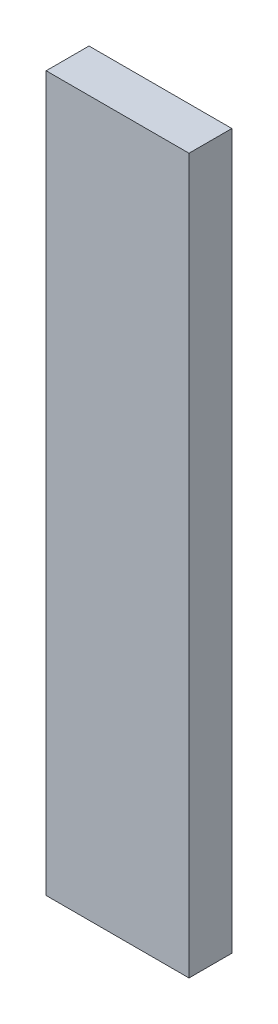
SolidWorks part; units mm, degrees
ref_plane "Alzado" through (0, 0, 0) normal (0, 0, 1) x (1, 0, 0)
ref_plane "Planta" through (0, 0, 0) normal (0, 1, 0) x (1, 0, 0)
ref_plane "Vista lateral" through (0, 0, 0) normal (1, 0, 0) x (0, 0, -1)
sketch "Model" plane through (0, 0, 0) normal (0, 0, 1) x (1, 0, 0)
  line L0 (20.8364, 1) -> (30.8364, 1)
  line L1 (20.8364, 51) -> (20.8364, 1)
  line L2 (30.8364, 51) -> (30.8364, 1)
  line L3 (20.8364, 51) -> (25.3364, 51)
  line L4 (25.3364, 51) -> (30.8364, 51)
extrude "Saliente-Extruir1" add sketch "Model" along normal blind 3
